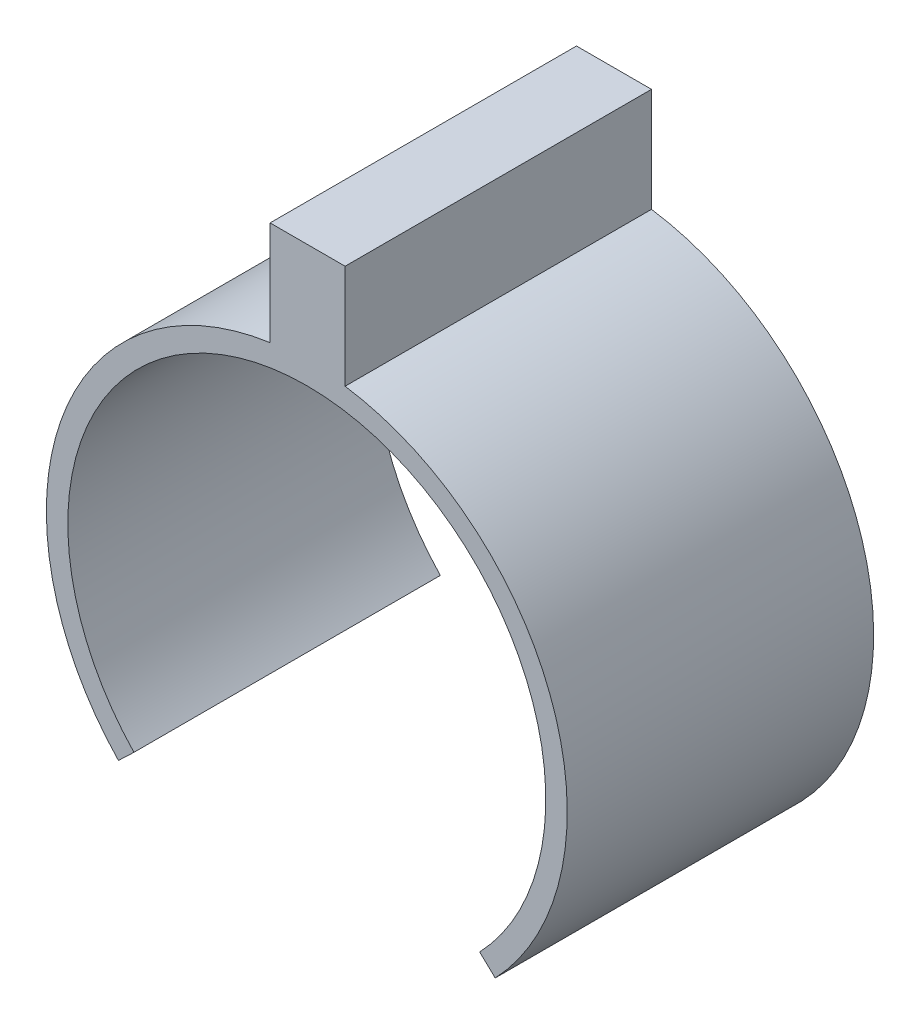
SolidWorks part; units mm, degrees
ref_plane "Front Plane" through (0, 0, 0) normal (0, 0, 1) x (1, 0, 0)
ref_plane "Top Plane" through (0, 0, 0) normal (0, 1, 0) x (1, 0, 0)
ref_plane "Right Plane" through (0, 0, 0) normal (1, 0, 0) x (0, 0, -1)
sketch "Sketch1" plane through (0, 0, 0) normal (0, 0, 1) x (1, 0, 0)
  circle A0 centre (0, 0) radius 3.9
  circle A1 centre (0, 0) radius 4.25
  dimension "D1" = 7.8
  dimension "D2" = 8.5
extrude "Boss-Extrude1" add sketch "Sketch1" along normal blind 5
sketch "Sketch2" plane through (0, 0, 5) normal (0, 0, 1) x (1, 0, 0)
  line L0 (0, 0) -> (0, -6.2681) construction
  line L1 (-3.0741, -2.9347) -> (-2.8209, -2.693)
  line L3 (3.0741, -2.9347) -> (2.8209, -2.693)
  circle A0 centre (0, 0) radius 4.25 construction
  circle A1 centre (0, 0) radius 3.9 construction
  arc A2 (-2.8209, -2.693) -> (2.8209, -2.693) centre (0, 0) ccw
  arc A3 (-3.0741, -2.9347) -> (3.0741, -2.9347) centre (0, 0) ccw
extrude "Cut-Extrude1" cut sketch "Sketch2" against normal blind 5
ref_plane "Plane1" through (0, 3.9, 0) normal (0, 1, 0) x (1, 0, 0)
sketch "Sketch3" plane through (0, 3.9, 0) normal (0, 1, 0) x (1, 0, 0)
  line L0 (4.25, 0) -> (-4.25, 0) construction
  line L2 (-0.5993, 0) -> (0.625, 0)
  line L3 (-0.5993, 0) -> (-0.5993, -5)
  line L4 (-0.5993, -5) -> (0.625, -5)
  line L5 (0.625, 0) -> (0.625, -5)
  line L6 (-4.25, -5) -> (4.25, -5) construction
extrude "Boss-Extrude2" add sketch "Sketch3" along normal blind 2
